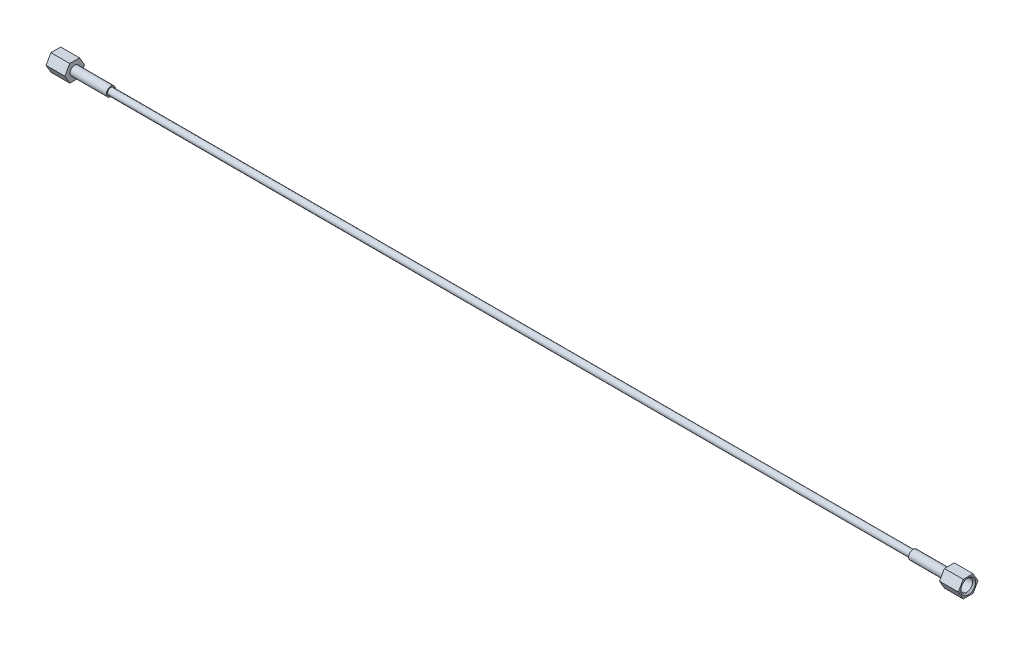
SolidWorks part; units mm, degrees
material "Alloy Steel"
ref_plane "Front Plane" through (0, 0, 0) normal (0, 0, 1) x (1, 0, 0)
ref_plane "Top Plane" through (0, 0, 0) normal (0, 1, 0) x (1, 0, 0)
ref_plane "Right Plane" through (0, 0, 0) normal (1, 0, 0) x (0, 0, -1)
ref_plane "Plane5" through (-6.858, 0, 0) normal (1, 0, 0) x (0, 0, -1)
sketch "Sketch5" plane through (-6.858, 0, 0) normal (1, 0, 0) x (0, 0, -1)
  line L0 (4.1061, 7.112) -> (-4.1061, 7.112)
  line L1 (-4.1061, 7.112) -> (-8.2122, 0)
  line L2 (-8.2122, 0) -> (-4.1061, -7.112)
  line L3 (-4.1061, -7.112) -> (4.1061, -7.112)
  line L4 (4.1061, -7.112) -> (8.2122, 0)
  line L5 (8.2122, 0) -> (4.1061, 7.112)
extrude "Extrude2" add sketch "Sketch5" along normal blind 15.748 separate body
hole_wizard "Hole2" positions "Sketch7" profile "Sketch6" legacy end condition up to next
sketch "Sketch7" plane through (8.89, 0, 0) normal (1, 0, 0) x (0, 0, -1)
  point P0 (0, 0)
sketch "Sketch6" plane through (8.89, 0, 0) normal (0, 1, 0) x (0, 0, -1)
  line L0 (0, 0) -> (0, 15.748)
  line L1 (0, 15.748) -> (3.8354, 15.748)
  line L2 (3.8354, 15.748) -> (3.8354, 9.5661)
  line L3 (3.8354, 9.5661) -> (4.9606, 8.89)
  line L4 (4.9606, 8.89) -> (4.9606, 0)
  line L5 (4.9606, 0) -> (0, 0)
  line L6 (0, -6.13) -> (0, 109.2824) construction
  line L7 (-3.8354, 9.5661) -> (-4.9606, 8.89) construction
  line L8 (0, 15.748) -> (-3.8354, 15.748) construction
  dimension "Diameter" = 7.6708
  dimension "Depth" = 15.748
  dimension "C-Drill Diameter" = 9.9212
  dimension "C-Drill Depth" = 8.89
  dimension "C-Drill Angle" = 118
chamfer "Chamfer2" distance 1.2402 angle 45 1 edges at (8.89, 0, -4.9606)
ref_plane "Plane4" through (0, 0, 0) normal (0, 0, -1) x (-1, 0, 0)
sketch "Sketch8" plane through (0, 0, 0) normal (0, 0, -1) x (-1, 0, 0)
  line L0 (0.6914, 3.81) -> (2.3854, 0.9906)
  line L1 (2.3854, 0.9906) -> (741.8346, 0.9906)
  line L2 (707.136, 3.81) -> (743.5286, 3.81)
  line L3 (707.136, 2.7686) -> (707.136, 3.81)
  line L4 (743.5286, 3.81) -> (741.8346, 0.9906)
  line L5 (707.136, 2.7686) -> (37.084, 2.7686)
  line L6 (37.084, 2.7686) -> (37.084, 3.81)
  line L7 (37.084, 3.81) -> (0.6914, 3.81)
  line L8 (0.6914, 0) -> (202.5086, 0) construction
  line L9 (372.11, 24.5048) -> (372.11, -25.5618) construction
  line L10 (6.858, 7.112) -> (6.858, 0) construction
  line L13 (0.6761, 3.8354) -> (0, 4.9606) construction
  dimension "D1" = 381
  dimension "D2" = 1.9812
  dimension "D3" = 5.5372
  dimension "D4" = 7.62
  dimension "D6" = 30.226
revolve "Revolve2" add sketch "Sketch8" angle 360 about L8
ref_plane "Plane6" through (-372.11, 0, 0) normal (1, 0, 0) x (0, 0, -1)
mirror "Mirror2" about plane through (-372.11, 0, 0) normal (1, 0, 0) of bodies 118
